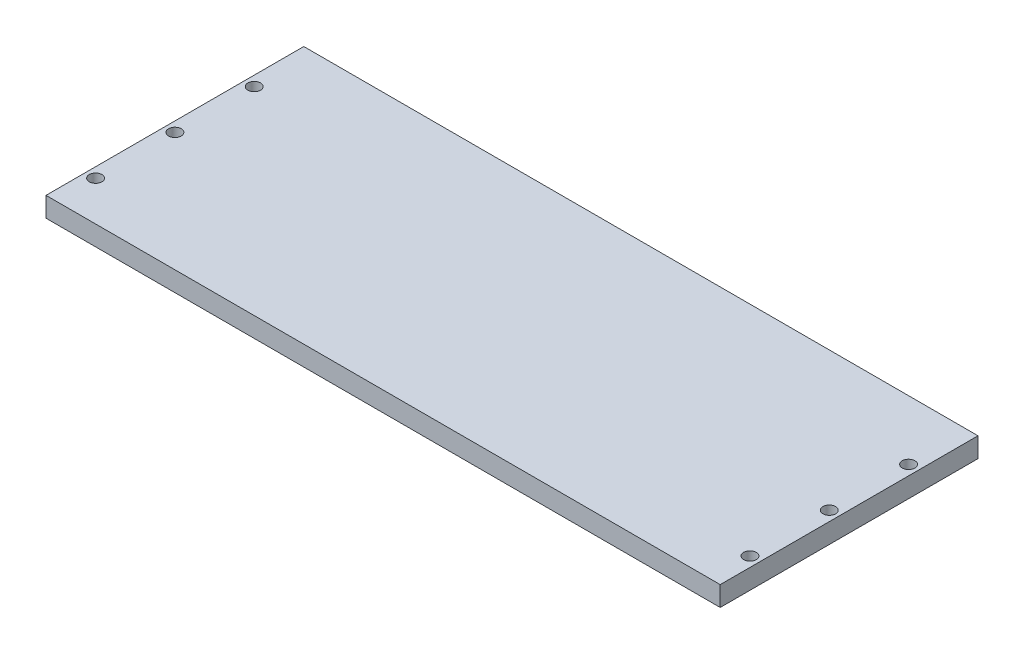
SolidWorks part; units mm, degrees
ref_plane "Front Plane" through (0, 0, 0) normal (0, 0, 1) x (1, 0, 0)
ref_plane "Top Plane" through (0, 0, 0) normal (0, 1, 0) x (1, 0, 0)
ref_plane "Right Plane" through (0, 0, 0) normal (1, 0, 0) x (0, 0, -1)
sketch "Sketch1" plane through (0, 0, 0) normal (0, 1, 0) x (1, 0, 0)
  line L0 (-82.5, 32.5) -> (-82.5, -32.5) construction
  line L1 (-85, 32.5) -> (85, 32.5)
  line L2 (-85, 32.5) -> (-85, -32.5)
  line L3 (-85, -32.5) -> (85, -32.5)
  line L4 (85, 32.5) -> (85, -32.5)
  line L5 (-85, 32.5) -> (85, -32.5) construction
  line L6 (-85, -32.5) -> (85, 32.5) construction
  line L7 (-85, 32.5) -> (-80, 32.5) construction
  line L8 (-85, 32.5) -> (-85, -32.5) construction
  line L9 (-85, -32.5) -> (-80, -32.5) construction
  line L10 (-80, 32.5) -> (-80, -32.5) construction
  line L11 (0, 0) -> (0, -32.5) construction
  circle A0 centre (-82.5, 17.5) radius 1.6
  circle A1 centre (-82.5, -2.5) radius 1.6
  circle A2 centre (-82.5, -22.5) radius 1.6
  circle A3 centre (82.5, -22.5) radius 1.6
  circle A4 centre (82.5, -2.5) radius 1.6
  circle A5 centre (82.5, 17.5) radius 1.6
  point P0 (0, 0)
  point P8 (-82.5, 32.5)
  point P11 (-82.5, 17.5)
  dimension "D6" = 3
  dimension "D1" = 170
  dimension "D2" = 65
  dimension "D3" = 5
  dimension "D4" = 2.5
  dimension "D5" = 15
extrude "Boss-Extrude1" add sketch "Sketch1" along normal blind 5
